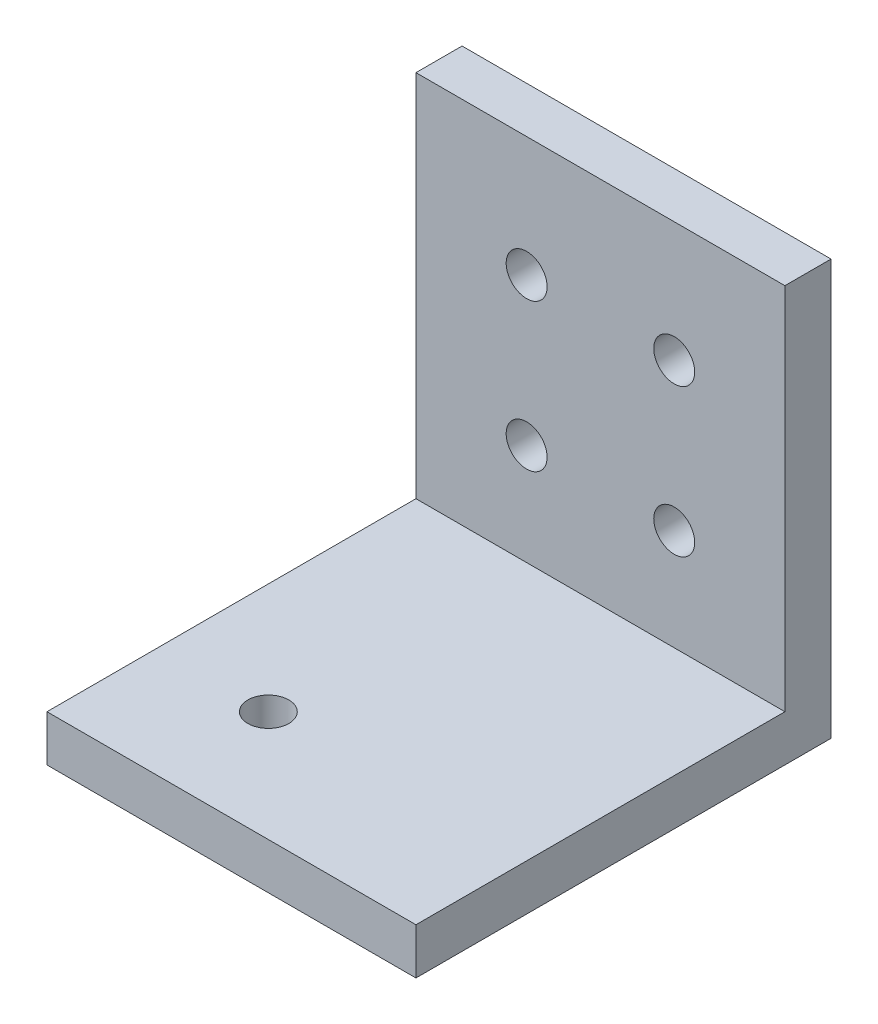
SolidWorks part; units mm, degrees
ref_plane "Front Plane" through (0, 0, 0) normal (0, 0, 1) x (1, 0, 0)
ref_plane "Top Plane" through (0, 0, 0) normal (0, 1, 0) x (1, 0, 0)
ref_plane "Right Plane" through (0, 0, 0) normal (1, 0, 0) x (0, 0, -1)
sketch "Sketch1" plane through (0, 0, 0) normal (0, 0, 1) x (1, 0, 0)
  line L1 (-12.7, 14.2875) -> (12.7, 14.2875)
  line L2 (-12.7, 14.2875) -> (-12.7, -14.2875)
  line L3 (-12.7, -14.2875) -> (12.7, -14.2875)
  line L4 (12.7, 14.2875) -> (12.7, -14.2875)
  line L5 (-12.7, 14.2875) -> (12.7, -14.2875) construction
  line L6 (-12.7, -14.2875) -> (12.7, 14.2875) construction
  point P0 (0, 0)
  dimension "D1" = 25.4
  dimension "D2" = 28.575
extrude "Boss-Extrude1" add sketch "Sketch1" along normal blind 3.175
sketch "Sketch2" plane through (0, 0, 3.175) normal (0, 0, 1) x (1, 0, 0)
  line L0 (12.7, -14.2875) -> (12.7, 14.2875) construction
  line L1 (-12.7, -14.2875) -> (12.7, -14.2875)
  line L2 (-12.7, -14.2875) -> (-12.7, -11.1125)
  line L3 (-12.7, -11.1125) -> (12.7, -11.1125)
  line L4 (12.7, -14.2875) -> (12.7, -11.1125)
  dimension "D1" = 3.175
extrude "Boss-Extrude2" add sketch "Sketch2" along normal blind 25.4
sketch "Sketch4" plane through (0, 0, 0) normal (0, 0, -1) x (-1, 0, 0)
  line L0 (-12.7, 14.2875) -> (12.7, 14.2875) construction
  line L1 (-12.7, -11.1125) -> (-12.7, 14.2875) construction
  circle A0 centre (-5.08, 6.0325) radius 1.4097
  dimension "D1" = 2.8194
  dimension "D2" = 8.255
  dimension "D3" = 7.62
extrude "Cut-Extrude1" cut sketch "Sketch4" against normal through all
pattern_linear "LPattern1" count 2 spacing 10.16 along (0, -1, 0) count 2 spacing 10.16 along (-1, 0, 0) of "Cut-Extrude1"
sketch "Sketch5" plane through (0, -11.1125, 0) normal (0, 1, 0) x (1, 0, 0)
  line L0 (-12.7, -28.575) -> (-12.7, -3.175) construction
  line L1 (12.7, -28.575) -> (-12.7, -28.575) construction
  circle A0 centre (-5.08, -20.955) radius 1.4097
  dimension "D1" = 2.8194
  dimension "D2" = 7.62
  dimension "D3" = 7.62
extrude "Cut-Extrude2" cut sketch "Sketch5" against normal through all
